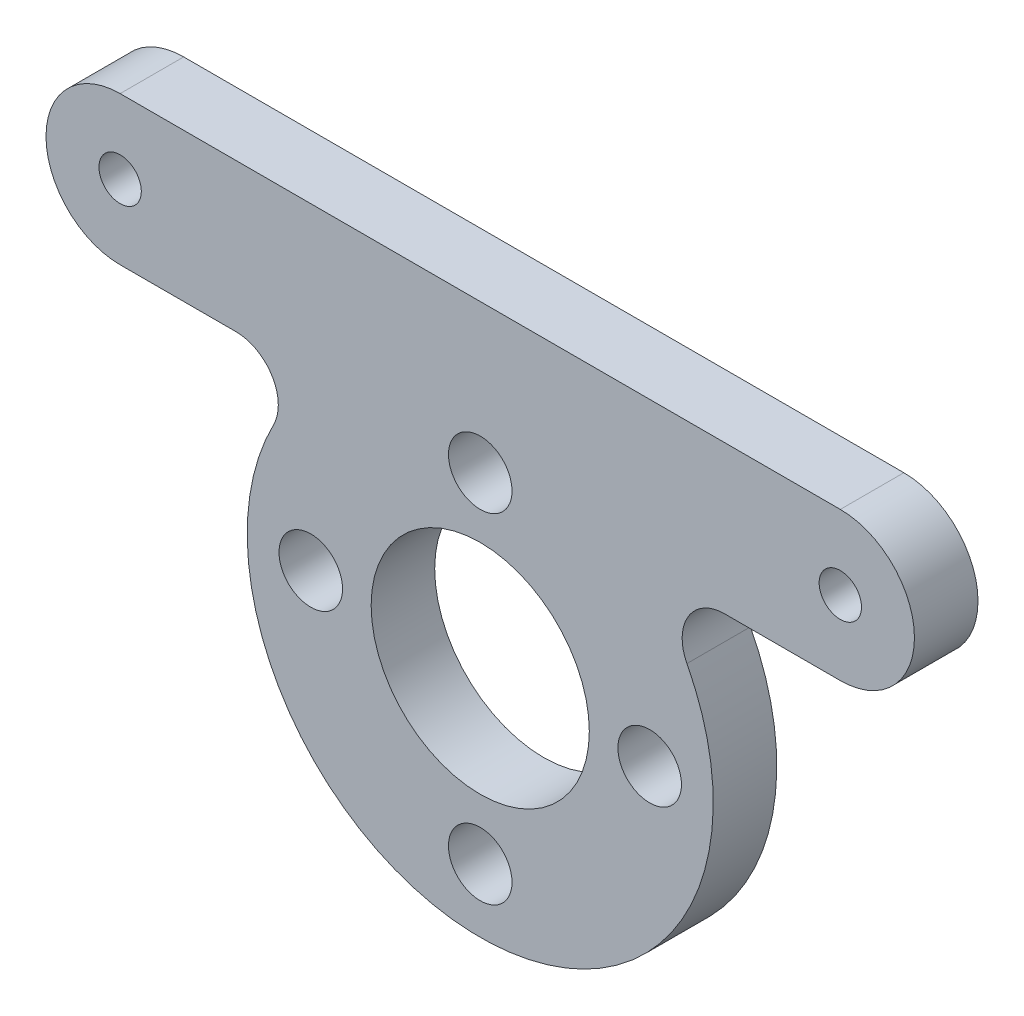
SolidWorks part; units mm, degrees
ref_plane "前视基准面" through (0, 0, 0) normal (0, 0, 1) x (1, 0, 0)
ref_plane "上视基准面" through (0, 0, 0) normal (0, 1, 0) x (1, 0, 0)
ref_plane "右视基准面" through (0, 0, 0) normal (1, 0, 0) x (0, 0, -1)
sketch "草图1" plane through (0, 0, 0) normal (0, 0, 1) x (1, 0, 0)
  line L0 (0, 0) -> (16, 0) construction
  line L1 (0, 0) -> (-16, 0) construction
  line L2 (-16, 0) -> (16, 0) construction
  line L3 (-17, 8) -> (-7.5498, 8)
  line L7 (17, 15) -> (-17, 15)
  line L8 (0, 0) -> (0, -4.727) construction
  line L9 (17, 8) -> (7.5498, 8)
  arc A0 (-7.5498, 8) -> (7.5498, 8) centre (0, 0) ccw
  arc A4 (-17, 15) -> (-17, 8) centre (-17, 11.5) ccw
  arc A5 (17, 15) -> (17, 8) centre (17, 11.5) cw
  point P6 (0, 0)
  point P14 (0, 15)
  dimension "D1" = 22
  dimension "D4" = 3.5
  dimension "D2" = 16
  dimension "D3" = 16
  dimension "D5" = 15
  dimension "D6" = 34
extrude "凸台-拉伸1" add sketch "草图1" along normal blind 3
sketch "草图2" plane through (0, 0, 3) normal (0, 0, 1) x (1, 0, 0)
  line L0 (0, 0) -> (8, 0) construction
  circle A0 centre (0, 0) radius 5.15
  circle A1 centre (8, 0) radius 1.5
  circle A2 centre (0, -8) radius 1.5
  circle A3 centre (-8, 0) radius 1.5
  circle A4 centre (0, 8) radius 1.5
  circle A5 centre (-17, 11.5) radius 1
  circle A6 centre (17, 11.5) radius 1
  point P14 (0, 0)
  dimension "D1" = 10.3
  dimension "D3" = 3
  dimension "D5" = 2
  dimension "D6" = 2
  dimension "D2" = 8
  dimension "D4" = 4
extrude "切除-拉伸1" cut sketch "草图2" against normal up to surface (3 mm away) up to face at (0, 7.1667, 0)
fillet "圆角1" radius 2 2 edges at (7.5498, 8, 1.5) (-7.5498, 8, 1.5)
